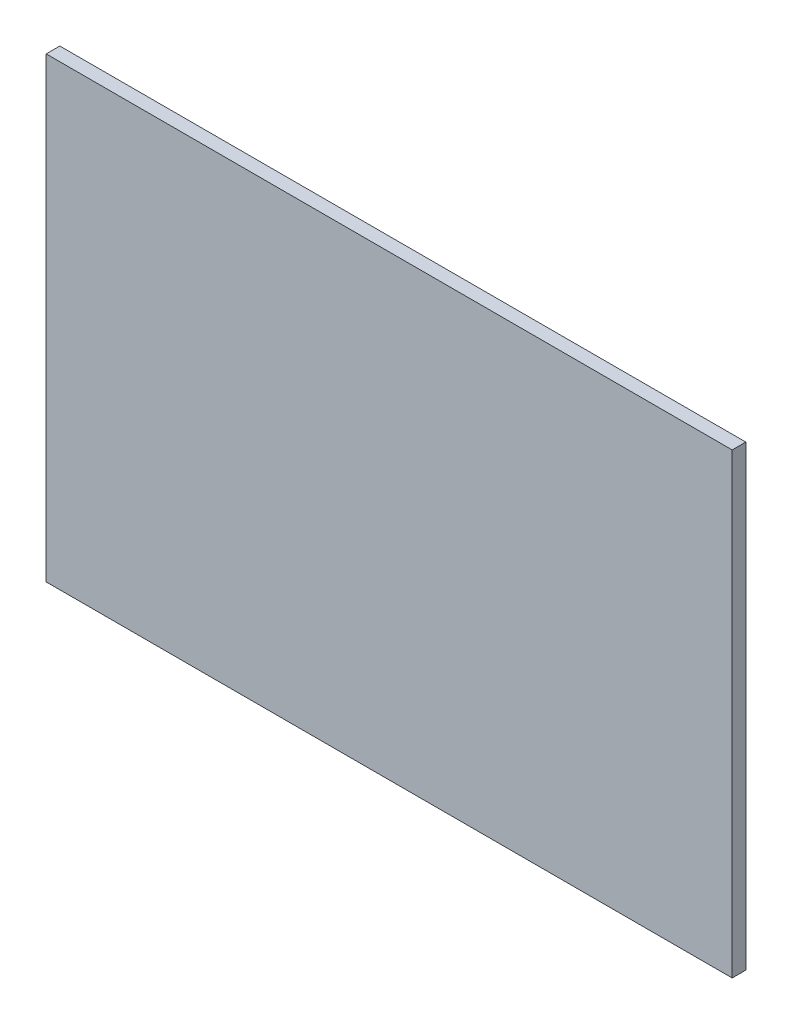
SolidWorks part; units mm, degrees
ref_plane "Front Plane" through (0, 0, 0) normal (0, 0, 1) x (1, 0, 0)
ref_plane "Top Plane" through (0, 0, 0) normal (0, 1, 0) x (1, 0, 0)
ref_plane "Right Plane" through (0, 0, 0) normal (1, 0, 0) x (0, 0, -1)
sketch "Sketch1" plane through (0, 0, 0) normal (0, 0, 1) x (1, 0, 0)
  line L1 (40.26, -26.84) -> (-40.26, -26.84)
  line L2 (40.26, -26.84) -> (40.26, 26.84)
  line L3 (40.26, 26.84) -> (-40.26, 26.84)
  line L4 (-40.26, -26.84) -> (-40.26, 26.84)
  line L5 (40.26, -26.84) -> (-40.26, 26.84) construction
  line L6 (40.26, 26.84) -> (-40.26, -26.84) construction
  point P0 (0, 0)
  dimension "D1" = 53.68
  dimension "D2" = 80.52
extrude "Boss-Extrude1" add sketch "Sketch1" along normal blind 1.6
